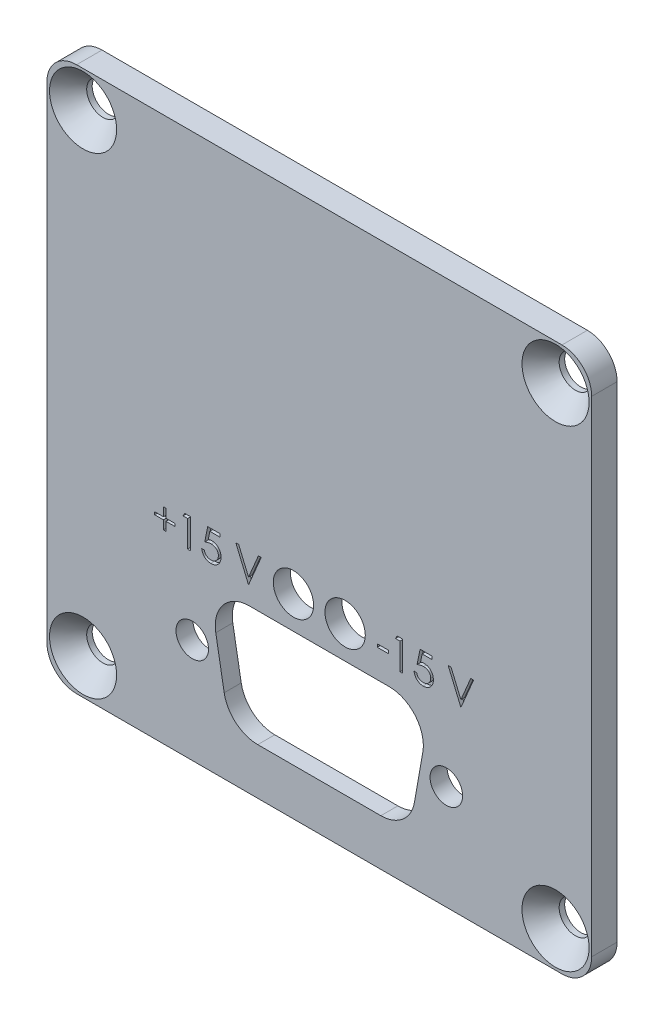
SolidWorks part; units mm, degrees
material "6061-T6 Al"
ref_plane "Front" through (0, 0, 0) normal (0, 0, 1) x (1, 0, 0)
ref_plane "Top" through (0, 0, 0) normal (0, 1, 0) x (1, 0, 0)
ref_plane "Right" through (0, 0, 0) normal (1, 0, 0) x (0, 0, -1)
sketch "Sketch1" plane through (0, 0, 0) normal (0, 0, 1) x (1, 0, 0)
  line L0 (-23.876, 26.797) -> (23.876, 26.797)
  line L1 (-26.797, 23.876) -> (-26.797, -23.876)
  line L2 (-23.876, -26.797) -> (23.876, -26.797)
  line L3 (26.797, 23.876) -> (26.797, -23.876)
  arc A0 (-26.797, -23.876) -> (-23.876, -26.797) centre (-23.876, -23.876) ccw
  arc A1 (23.876, -26.797) -> (26.797, -23.876) centre (23.876, -23.876) ccw
  arc A2 (23.876, 26.797) -> (26.797, 23.876) centre (23.876, 23.876) cw
  arc A3 (-26.797, 23.876) -> (-23.876, 26.797) centre (-23.876, 23.876) cw
  point P12 (0, 26.797)
  point P14 (-26.797, 0)
  dimension "D1" = 2.921
  dimension "D3" = 53.594
extrude "Boss-Extrude1" add sketch "Sketch1" along normal mid plane 2.5
hole_wizard "CSK for #4 Flat Head Machine Screw1" positions "Sketch6" profile "Sketch5" countersink size "#4" standard "ANSI Inch" end condition through all
sketch "Sketch6" plane through (0, 0, 1.25) normal (0, 0, 1) x (1, 0, 0)
  line L0 (-23.241, 23.241) -> (23.241, -23.241) construction
  line L1 (-23.241, 23.241) -> (23.241, 23.241) construction
  line L2 (23.241, 23.241) -> (23.241, -23.241) construction
  point P0 (-23.241, 23.241)
  point P1 (23.241, -23.241)
  point P6 (23.241, 23.241)
  point P10 (-23.241, -23.241)
  dimension "D1" = 46.482
sketch "Sketch5" plane through (-23.241, 23.241, 1.25) normal (1, 0, 0) x (0, -1, 0)
  line L0 (0, 0) -> (0, 2.5)
  line L1 (0, 2.5) -> (1.6002, 2.5)
  line L2 (1.6002, 2.5) -> (1.6002, 1.9577)
  line L3 (1.6002, 1.9577) -> (3.302, 0)
  line L5 (3.302, 0) -> (0, 0)
  line L6 (-1.6002, 1.9577) -> (-3.302, 0) construction
  line L11 (0, -6.35) -> (0, 107.95) construction
  dimension "Thru Hole Dia." = 3.2004
  dimension "Thru Hole Depth" = 2.5
  dimension "Near C'Sink Dia." = 6.604
  dimension "Near C'Sink Angle" = 82
sketch "Sketch7" plane through (0, 0, -1.25) normal (0, 0, 1) x (1, 0, 0)
  line L0 (0, -16.5202) -> (0, -24.1402) construction
  line L1 (-13.081, -8.2652) -> (0, -14.6152) construction
  line L2 (-12.5, -16.5202) -> (0, -16.5202) construction
  line L3 (0, -16.5202) -> (12.5, -16.5202) construction
  line L4 (13.081, -5.0902) -> (-13.081, -5.0902)
  line L5 (16.256, -8.2652) -> (16.256, -20.9652)
  line L6 (13.081, -24.1402) -> (-13.081, -24.1402)
  line L7 (-16.256, -8.2652) -> (-16.256, -20.9652)
  line L8 (0, -14.6152) -> (13.081, -20.9652) construction
  line L9 (-23.876, -26.797) -> (23.876, -26.797) construction
  arc A0 (-13.081, -24.1402) -> (-16.256, -20.9652) centre (-13.081, -20.9652) cw
  arc A1 (-13.081, -5.0902) -> (-16.256, -8.2652) centre (-13.081, -8.2652) ccw
  arc A2 (13.081, -5.0902) -> (16.256, -8.2652) centre (13.081, -8.2652) cw
  arc A3 (16.256, -20.9652) -> (13.081, -24.1402) centre (13.081, -20.9652) cw
  point P13 (-16.256, -5.0902)
  point P19 (16.256, -24.1402)
  dimension "D1" = 25
  dimension "D2" = 11.43
  dimension "D5" = 3.175
  dimension "D3" = 16.5202
  dimension "D4" = 19.05
  dimension "D6" = 32.512
  dimension "D7" = 12.1818
extrude "Connector Land" cut sketch "Sketch7" along direction (0, 0, -1) on the side of the normal offset from surface (0.8236 mm away) 1.6764
hole_wizard "#4 Clearance Hole1" positions "Sketch9" profile "Sketch8" hole size "#4" standard "ANSI Inch" end condition through all
sketch "Sketch9" plane through (0, 0, -0.4264) normal (0, 0, -1) x (-1, 0, 0)
  point P0 (12.5, -16.5202)
  point P2 (-12.5, -16.5202)
sketch "Sketch8" plane through (-12.5, -16.5202, -0.4264) normal (1, 0, 0) x (0, 1, 0)
  line L0 (0, 0) -> (0, 1.6764)
  line L1 (0, 1.6764) -> (1.6002, 1.6764)
  line L2 (1.6002, 1.6764) -> (1.6002, 0)
  line L5 (1.6002, 0) -> (0, 0)
  line L11 (0, -6.35) -> (0, 107.95) construction
  dimension "Thru Hole Dia." = 3.2004
  dimension "Thru Hole Depth" = 1.6764
sketch "Sketch10" plane through (0, 0, 1.25) normal (0, 0, 1) x (1, 0, 0)
  line L0 (0, -22.2225) -> (0, -16.5202) construction
  line L1 (-2.54, -7.62) -> (0, 0) construction
  line L2 (12.4968, -16.5202) -> (-12.4968, -16.5202) construction
  line L3 (0, 0) -> (2.54, -7.62) construction
  line L4 (-9.3567, -19.4519) -> (-10.1853, -14.7529)
  line L5 (9.3567, -19.4519) -> (10.1853, -14.7529)
  line L6 (6.0548, -22.2225) -> (-6.0548, -22.2225)
  line L7 (6.8834, -10.8179) -> (-6.8834, -10.8179)
  line L8 (0, -16.5202) -> (0, -10.8179) construction
  line L9 (-16.4211, -9.017) -> (-0.5461, -9.017) construction
  line L10 (-0.5461, -9.017) -> (15.3289, -9.017) construction
  line L12 (-15.4051, -22.794) -> (-15.4051, -10.2464) construction
  line L13 (-15.4051, -22.794) -> (15.4051, -22.794) construction
  line L14 (15.4051, -22.794) -> (15.4051, -10.2464) construction
  line L15 (-15.4051, -10.2464) -> (15.4051, -10.2464) construction
  circle A0 centre (12.4968, -16.5202) radius 1.6002 construction
  circle A1 centre (-12.4968, -16.5202) radius 1.6002 construction
  arc A2 (10.1853, -14.7529) -> (6.8834, -10.8179) centre (6.8834, -14.1707) ccw
  arc A3 (-10.1853, -14.7529) -> (-6.8834, -10.8179) centre (-6.8834, -14.1707) cw
  arc A4 (-9.3567, -19.4519) -> (-6.0548, -22.2225) centre (-6.0548, -18.8697) ccw
  arc A5 (9.3567, -19.4519) -> (6.0548, -22.2225) centre (6.0548, -18.8697) cw
  circle A6 centre (-2.54, -7.62) radius 1.9844
  circle A7 centre (2.54, -7.62) radius 1.9844
  circle A8 centre (23.241, -23.241) radius 1.6002 construction
  point P16 (10.8791, -10.8179)
  point P19 (-10.8791, -10.8179)
  point P22 (-8.8682, -22.2225)
  point P25 (8.8682, -22.2225)
  dimension "D2" = 5.08
  dimension "D3" = 24.9936
  dimension "D5" = 2.5833
  dimension "D8" = 3.3528
  dimension "D11" = 0.9831
  dimension "D10" = 20.4724
  dimension "D12" = 3.9688
  dimension "D4" = 20
  dimension "D6" = 11.4046
  dimension "D7" = 12.5476
  dimension "D9" = 30.8102
  dimension "D13" = 7.62
  dimension "D14" = 1.397
  dimension "D15" = 31.75
  dimension "D16" = 0.5461
extrude "Connector Cut-out" cut sketch "Sketch10" against normal through all
sketch "Sketch12" plane through (0, 0, 1.25) normal (0, 0, 1) x (1, 0, 0)
  text T0 "+15 V" font "Century Gothic" height in points 11
  text T1 "-15 V" font "Century Gothic" height in points 11
extrude "Cut-Extrude1" cut sketch "Sketch12" against normal blind 0.381
